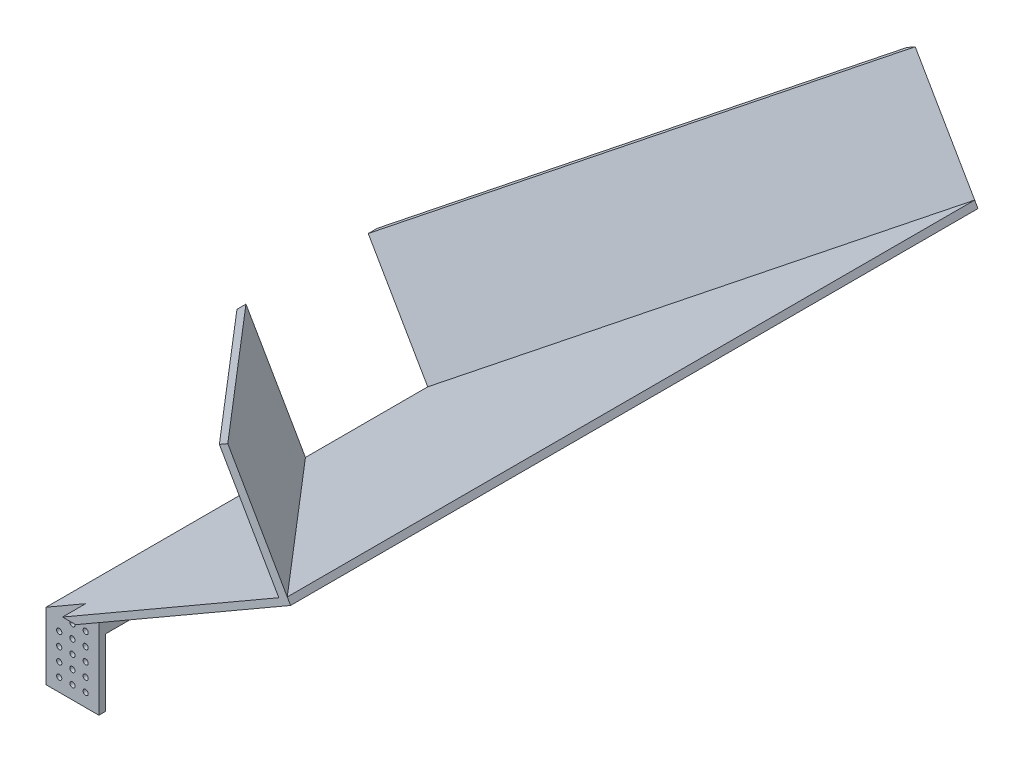
SolidWorks part; units mm, degrees
ref_plane "Front Plane" through (0, 0, 0) normal (0, 0, 1) x (1, 0, 0)
ref_plane "Top Plane" through (0, 0, 0) normal (0, 1, 0) x (1, 0, 0)
ref_plane "Right Plane" through (0, 0, 0) normal (1, 0, 0) x (0, 0, -1)
sketch "Sketch1" plane through (0, 0, 0) normal (0, 0, 1) x (1, 0, 0)
  line L0 (0, 64.4823) -> (254, 211.1293)
  line L1 (0, 0) -> (50.8, 0) construction
  line L2 (0, 0) -> (0, 203.2) construction
  line L3 (0, 203.2) -> (50.8, 203.2) construction
  line L4 (50.8, 0) -> (50.8, 203.2) construction
  line L5 (0, 57.15) -> (257.175, 205.6301)
  line L6 (3.175, 58.9831) -> (257.175, 205.6301) construction
  line L7 (257.175, 205.6301) -> (254, 211.1293)
  line L8 (0, 64.4823) -> (0, 57.15)
  line L9 (0, 57.15) -> (0, 0)
  line L10 (0, 0) -> (50.8, 0)
  line L11 (50.8, 0) -> (50.8, 86.4794)
  line L12 (12.7, 12.7) -> (25.4, 12.7) construction
  line L13 (12.7, 12.7) -> (12.7, 25.4) construction
  circle A0 centre (12.7, 12.7) radius 2.4892
  circle A1 centre (25.4, 12.7) radius 2.4892
  circle A2 centre (38.1, 12.7) radius 2.4892
  circle A3 centre (25.4, 25.4) radius 2.4892
  circle A4 centre (38.1, 25.4) radius 2.4892
  circle A5 centre (25.4, 38.1) radius 2.4892
  circle A6 centre (38.1, 38.1) radius 2.4892
  circle A7 centre (25.4, 50.8) radius 2.4892
  circle A8 centre (38.1, 50.8) radius 2.4892
  circle A9 centre (25.4, 63.5) radius 2.4892
  circle A10 centre (38.1, 63.5) radius 2.4892
  circle A11 centre (25.4, 76.2) radius 2.4892
  circle A12 centre (38.1, 76.2) radius 2.4892
  circle A13 centre (25.4, 88.9) radius 2.4892
  circle A14 centre (38.1, 88.9) radius 2.4892
  circle A15 centre (12.7, 25.4) radius 2.4892
  circle A16 centre (12.7, 38.1) radius 2.4892
  circle A17 centre (12.7, 50.8) radius 2.4892
  circle A18 centre (12.7, 63.5) radius 2.4892
  circle A19 centre (12.7, 76.2) radius 2.4892
  circle A20 centre (12.7, 88.9) radius 2.4892
  dimension "D6" = 12.7
  dimension "D8" = 4.9784
  dimension "D1" = 50.8
  dimension "D2" = 203.2
  dimension "D3" = 30
  dimension "D4" = 254
  dimension "D7" = 12.7
  dimension "D11" = 90
  dimension "D12" = 12.7
  dimension "D13" = 12.7
  dimension "D14" = 57.15
  dimension "D5" = 6.35
  dimension "D9" = 3
  dimension "D10" = 7
extrude "Boss-Extrude1" add sketch "Sketch1" along normal blind 660.4 contours A18 L5 L7 L0 A14 L8 A11 | A11 | L5 A18 | A18 L5 L9 L10 L11 A17 A16 A15 A12 A10 A9 A8 A7 A6 A5 A4 A3 A2 A1 A0 | A12 | L5 A18 | L0 A14
sketch "Sketch2" plane through (0, 0, 0) normal (-1, 0, 0) x (0, 0, 1)
  line L0 (660.4, 64.4823) -> (0, 64.4823) construction
  line L1 (34.925, 64.4823) -> (631.825, 64.4823)
  line L2 (34.925, 64.4823) -> (34.925, 0)
  line L3 (34.925, 0) -> (631.825, 0)
  line L4 (631.825, 64.4823) -> (631.825, 0)
  line L5 (660.4, 0) -> (0, 0) construction
  line L8 (660.4, 64.4823) -> (660.4, 0) construction
  line L11 (0, 86.4794) -> (28.575, 86.4794)
  line L12 (0, 86.4794) -> (0, 0)
  line L13 (0, 0) -> (28.575, 0)
  line L14 (28.575, 86.4794) -> (28.575, 0)
  line L15 (660.4, 86.4794) -> (638.175, 86.4794)
  line L16 (660.4, 86.4794) -> (660.4, 0)
  line L17 (660.4, 0) -> (638.175, 0)
  line L18 (638.175, 86.4794) -> (638.175, 0)
  point P22 (0, 0)
  point P23 (0, 85.7202)
  point P26 (0, 0)
  dimension "D1" = 28.575
  dimension "D2" = 596.9
  dimension "D3" = 6.35
  dimension "D4" = 6.35
extrude "Cut-Extrude1" cut sketch "Sketch2" against normal blind 660.4
sketch "Sketch4" plane through (-27.9217, 48.3618, 0) normal (-0.5, 0.866, 0) x (0.866, 0.5, 0)
  line L0 (325.5351, 0) -> (32.2412, -271.4625)
  line L1 (32.2412, -631.825) -> (32.2412, -34.925) construction
  line L2 (32.2412, -330.2) -> (325.5351, -330.2) construction
  line L3 (325.5351, -660.4) -> (325.5351, 0) construction
  line L4 (316.1868, 0) -> (32.2412, -262.81)
  line L5 (321.2218, 4.6602) -> (27.9278, -266.8023) construction
  line L6 (76.2353, 0) -> (325.5351, 0) construction
  line L7 (32.2412, -271.4625) -> (32.2412, -262.81)
  line L8 (325.5351, 0) -> (316.1868, 0)
  line L9 (325.5351, -660.4) -> (316.1868, -660.4)
  line L10 (32.2412, -388.9375) -> (32.2412, -397.59)
  line L11 (316.1868, -660.4) -> (32.2412, -397.59)
  line L12 (325.5351, -660.4) -> (32.2412, -388.9375)
  point P5 (32.2412, -333.375)
  point P8 (0, 0)
  point P17 (32.2412, -330.2)
  point P22 (32.2412, -330.2)
  dimension "D1" = 61.9125
  dimension "D2" = 6.35
extrude "Boss-Extrude3" add sketch "Sketch4" along normal blind 114.3
